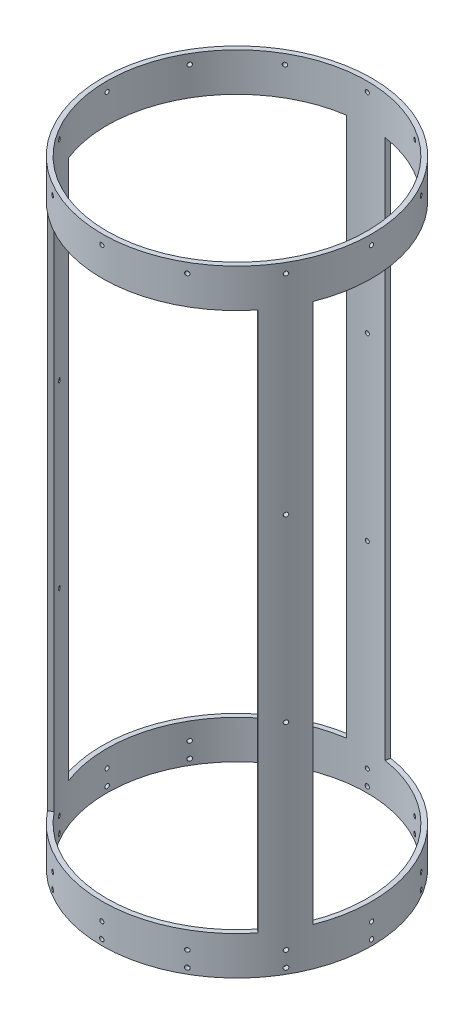
SolidWorks part; units mm, degrees
material "6061-T6 (SS)"
ref_plane "Front Plane" through (0, 0, 0) normal (0, 0, 1) x (1, 0, 0)
ref_plane "Top Plane" through (0, 0, 0) normal (0, 1, 0) x (1, 0, 0)
ref_plane "Right Plane" through (0, 0, 0) normal (1, 0, 0) x (0, 0, -1)
sketch "Sketch1" plane through (0, 0, 0) normal (0, 1, 0) x (1, 0, 0)
  circle A0 centre (0, 0) radius 88.9
  circle A1 centre (0, 0) radius 85.725
  dimension "D1" = 177.8
  dimension "D2" = 171.45
extrude "Boss-Extrude1" add sketch "Sketch1" along normal mid plane 406.4
sketch "Sketch6" plane through (0, -203.2, 0) normal (0, -1, 0) x (-1, 0, 0)
  line L0 (82.7901, -32.3885) -> (79.8333, -31.2317)
  line L1 (13.1222, 87.9262) -> (12.6536, 84.786)
  line L2 (0, 0) -> (0, 85.725) construction
  line L3 (-97.8543, 0) -> (97.8543, 0) construction
  line L4 (0, 0) -> (12.6536, 84.786) construction
  arc A0 (13.1222, 87.9262) -> (82.7901, -32.3885) centre (0, 0) cw
  circle A1 centre (0, 0) radius 88.9 construction
  arc A2 (12.6536, 84.786) -> (79.8333, -31.2317) centre (0, 0) cw
  circle A3 centre (0, 0) radius 85.725 construction
  arc A4 (0, 85.725) -> (12.6536, 84.786) centre (0, 0) cw construction
  dimension "D1" = 153.924
  dimension "D2" = 12.7
extrude "Cut-Extrude5" cut sketch "Sketch6" against normal blind 355.6 from offset 25.4 offset against normal yes
pattern_circular "CirPattern5" count 3 over 360 about axis through (0, 0, 0) along (0, 1, 0) of "Cut-Extrude5"
ref_plane "Plane1" through (0, 0, -88.9) normal (0, 0, -1) x (-1, 0, 0)
sketch "Sketch3" plane through (0, 0, 0) normal (0, 0, -1) x (-1, 0, 0)
  line L1 (-88.9, -203.2) -> (88.9, -203.2) construction
  line L3 (-12.8692, 177.8) -> (-12.8692, -177.8) construction
  circle A0 centre (-0.1692, -199.39) radius 1.4351
  circle A1 centre (-0.1692, -189.23) radius 1.3525
  dimension "D1" = 3.81
  dimension "D2" = 2.8702
  dimension "D3" = 2.7051
  dimension "D4" = 12.7
  dimension "D5" = 10.16
extrude "Cut-Extrude2" cut sketch "Sketch3" along normal up to surface (88.891 mm away)
pattern_circular "CirPattern2" count 12 over 360 about axis through (0, 203.2, 0) along (0, -1, 0) of "Cut-Extrude2"
sketch "Sketch4" plane through (0, 0, -88.9) normal (0, 0, -1) x (-1, 0, 0)
  line L1 (88.9, 203.2) -> (-88.9, 203.2) construction
  circle A0 centre (-0.1692, 196.85) radius 1.3525
  dimension "D1" = 2.7051
  dimension "D2" = 6.35
extrude "Cut-Extrude3" cut sketch "Sketch4" against normal blind 15.24
pattern_circular "CirPattern3" count 12 over 360 about axis through (0, 203.2, 0) along (0, 1, 0) of "Cut-Extrude3"
ref_plane "Plane2" through (0, 0, 88.9) normal (0, 0, 1) x (1, 0, 0)
sketch "Sketch5" plane through (0, 0, 88.9) normal (0, 0, 1) x (1, 0, 0)
  line L0 (-88.9, 177.8) -> (-13.1222, 177.8) construction
  line L1 (88.9, -177.8) -> (13.3458, -177.8) construction
  circle A0 centre (0.1692, 59.2667) radius 1.3526
  circle A1 centre (0.1692, -59.2667) radius 1.3526
  dimension "D1" = 118.5333
  dimension "D2" = 118.5333
  dimension "D3" = 2.7051
  dimension "D4" = 2.7051
extrude "Cut-Extrude4" cut sketch "Sketch5" against normal up to surface (177.787 mm away)
pattern_circular "CirPattern4" count 3 over 360 about axis through (0, 203.2, 0) along (0, -1, 0) of "Cut-Extrude4"
